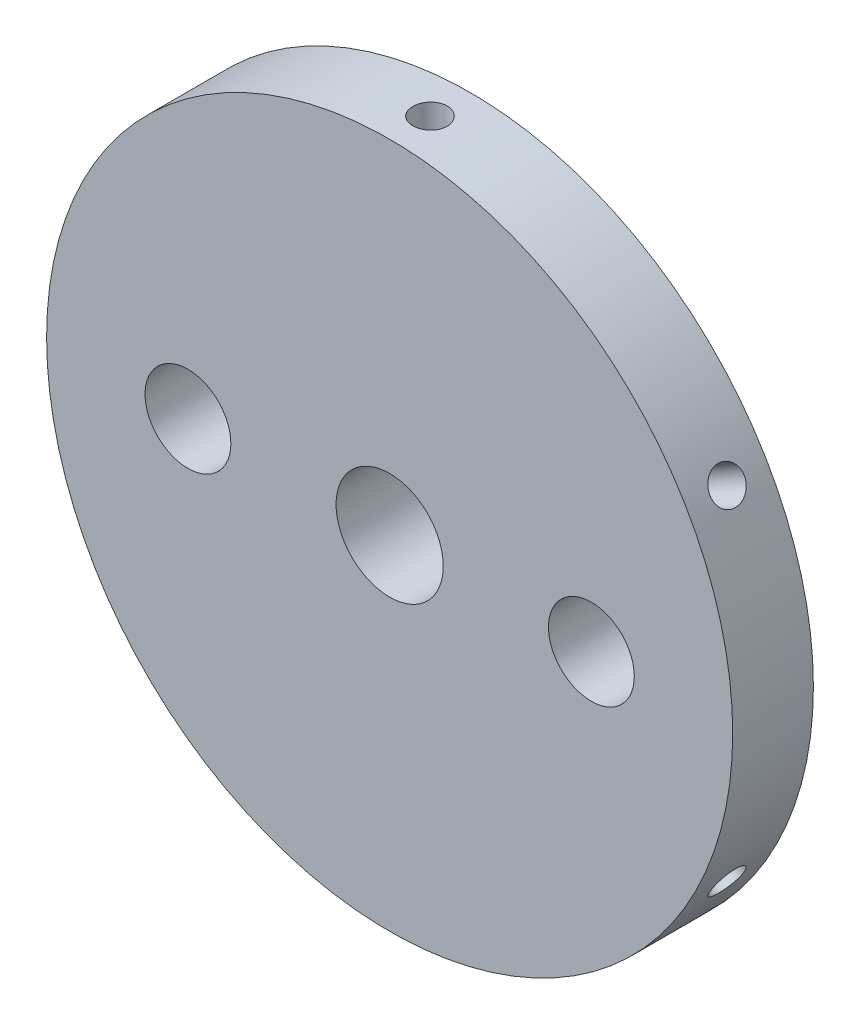
SolidWorks part; units mm, degrees
ref_plane "Front Plane" through (0, 0, 0) normal (0, 0, 1) x (1, 0, 0)
ref_plane "Top Plane" through (0, 0, 0) normal (0, 1, 0) x (1, 0, 0)
ref_plane "Right Plane" through (0, 0, 0) normal (1, 0, 0) x (0, 0, -1)
sketch "Sketch2" plane through (0, 0, 0) normal (0, 0, 1) x (1, 0, 0)
  circle A0 centre (0, 0) radius 27
  dimension "D1" = 54
extrude "Boss-Extrude1" add sketch "Sketch2" along normal mid plane 6.35
sketch "Sketch3" plane through (0, 0, 3.175) normal (0, 0, 1) x (1, 0, 0)
  point P0 (0, 0)
hole_wizard "5/16 Clearance Hole1" positions "Sketch3" profile "Sketch4" hole size "5/16" standard "ANSI Inch" end condition through all
sketch "Sketch4" plane through (0, 0, 3.175) normal (1, 0, 0) x (0, -1, 0)
  line L0 (0, 0) -> (0, 6.35)
  line L1 (0, 6.35) -> (4.2164, 6.35)
  line L2 (4.2164, 6.35) -> (4.2164, 0)
  line L5 (4.2164, 0) -> (0, 0)
  line L11 (0, -6.35) -> (0, 107.95) construction
  dimension "Thru Hole Dia." = 8.4328
  dimension "Thru Hole Depth" = 6.35
sketch "Sketch5" plane through (0, 0, 3.175) normal (0, 0, 1) x (1, 0, 0)
  line L1 (-1000, 0) -> (49000, 0) construction
  point P8 (-15.875, 0)
  point P10 (15.875, 0)
  point P18 (0, 0)
  point P19 (0, 0)
  point P20 (15.875, 0)
  dimension "D1" = 15.875
  dimension "D2" = 15.875
  dimension "D3" = 31.75
hole_wizard "1/4 Clearance Hole1" positions "Sketch5" profile "Sketch7" hole size "1/4" standard "ANSI Inch" end condition through all
sketch "Sketch7" plane through (-15.875, 0, 3.175) normal (1, 0, 0) x (0, -1, 0)
  line L0 (0, 0) -> (0, 6.35)
  line L1 (0, 6.35) -> (3.3782, 6.35)
  line L2 (3.3782, 6.35) -> (3.3782, 0)
  line L5 (3.3782, 0) -> (0, 0)
  line L11 (0, -6.35) -> (0, 107.95) construction
  dimension "Thru Hole Dia." = 6.7564
  dimension "Thru Hole Depth" = 6.35
ref_plane "Plane1" through (0, 27, 0) normal (0, 1, 0) x (1, 0, 0)
sketch "Sketch8" plane through (0, 27, 0) normal (0, 1, 0) x (1, 0, 0)
  point P0 (0, 0)
hole_wizard "Tap Drill for #6-32 Tap1" positions "Sketch8" profile "Sketch9" hole size "#6-32" standard "ANSI Inch"
sketch "Sketch9" plane through (0, 27, 0) normal (1, 0, 0) x (0, 0, 1)
  line L0 (0, 0) -> (0, 7.1627)
  line L1 (0, 7.1627) -> (1.3525, 6.35)
  line L2 (1.3525, 6.35) -> (1.3525, 0)
  line L5 (1.3525, 0) -> (0, 0)
  line L10 (0, 7.1627) -> (-1.3526, 6.35) construction
  line L11 (0, -6.35) -> (0, 107.95) construction
  dimension "Hole Dia." = 2.7051
  dimension "Hole Depth" = 6.35
  dimension "Drill Angle" = 118
pattern_circular "CirPattern1" count 6 over 360 about axis through (0, 0, 3.175) along (0, 0, 1) of "Tap Drill for #6-32 Tap1"
